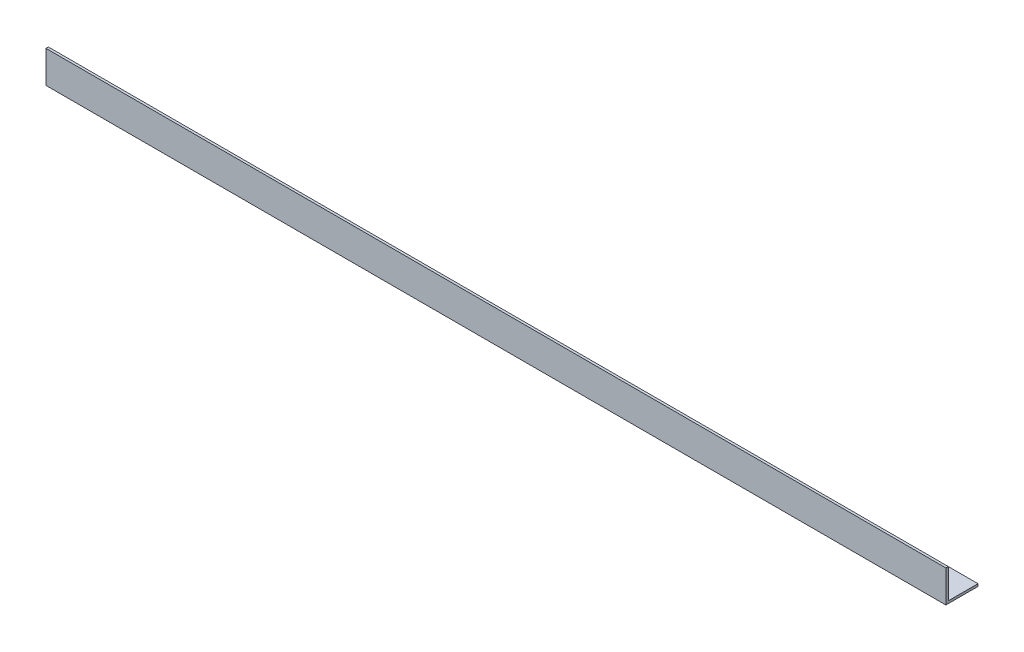
SolidWorks part; units mm, degrees
ref_plane "Спереди" through (0, 0, 0) normal (0, 0, 1) x (1, 0, 0)
ref_plane "Сверху" through (0, 0, 0) normal (0, 1, 0) x (1, 0, 0)
ref_plane "Справа" through (0, 0, 0) normal (1, 0, 0) x (0, 0, -1)
sketch "Эскиз1" plane through (0, 0, 0) normal (1, 0, 0) x (0, 0, -1)
  line L0 (0, 0) -> (0, 40)
  line L1 (0, 0) -> (40, 0)
extrude "Вытянуть-Тонкостенный1" add sketch "Эскиз1" along normal blind 1120 thin
